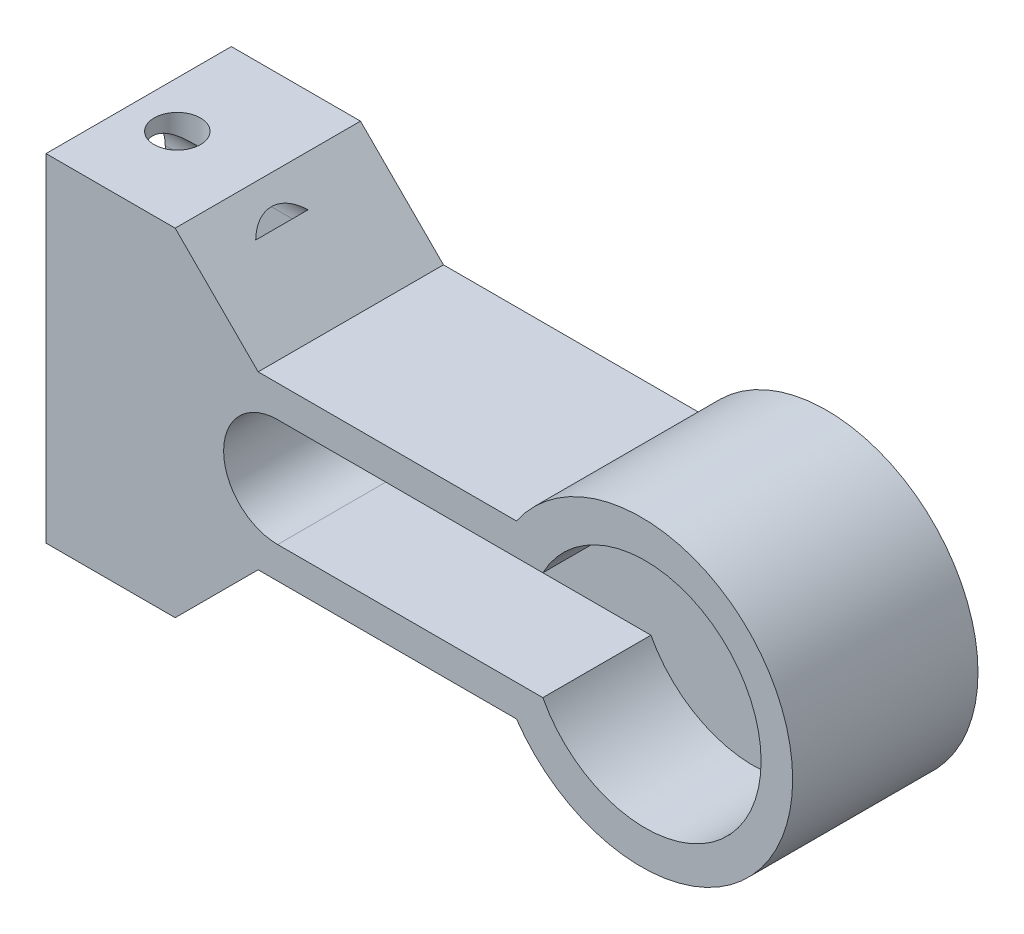
SolidWorks part; units mm, degrees
ref_plane "Front Plane" through (0, 0, 0) normal (0, 0, 1) x (1, 0, 0)
ref_plane "Top Plane" through (0, 0, 0) normal (0, 1, 0) x (1, 0, 0)
ref_plane "Right Plane" through (0, 0, 0) normal (1, 0, 0) x (0, 0, -1)
sketch "Sketch1" plane through (0, 0, 0) normal (0, 0, 1) x (1, 0, 0)
  line L1 (25, -15) -> (-25, -15)
  line L2 (25, -15) -> (25, 15)
  line L3 (25, 15) -> (-25, 15)
  line L4 (-25, -15) -> (-25, 15)
  line L5 (25, -15) -> (-25, 15) construction
  line L6 (25, 15) -> (-25, -15) construction
  point P0 (0, 0)
  dimension "D1" = 30
  dimension "D2" = 50
extrude "Boss-Extrude1" add sketch "Sketch1" along normal blind 15
sketch "Sketch2" plane through (-25, 0, 0) normal (-1, 0, 0) x (0, 0, 1)
  line L0 (6.7287, 7.5168) -> (6.7287, -7.9271) construction
  line L1 (9.1787, 7.5168) -> (9.1787, -7.9271)
  line L2 (4.2787, 7.5168) -> (4.2787, -7.9271)
  arc A0 (9.1787, 7.5168) -> (4.2787, 7.5168) centre (6.7287, 7.5168) ccw
  arc A1 (4.2787, -7.9271) -> (9.1787, -7.9271) centre (6.7287, -7.9271) ccw
  circle A2 centre (6.7287, -0.2052) radius 4.5
  point P2 (6.7287, -0.2052)
  dimension "D1" = 2.45
extrude "Cut-Extrude1" cut sketch "Sketch2" against normal blind 10
sketch "Sketch4" plane through (0, 0, 15) normal (0, 0, 1) x (1, 0, 0)
  line L0 (-10, 0) -> (13.8, 0) construction
  line L1 (-10, 3.5) -> (13.8, 3.5)
  line L2 (-10, -3.5) -> (13.8, -3.5)
  line L3 (25, -15) -> (25, 15) construction
  arc A0 (-10, 3.5) -> (-10, -3.5) centre (-10, 0) ccw
  arc A1 (13.8, -3.5) -> (13.8, 3.5) centre (13.8, 0) ccw
  circle A2 centre (13.8, 0) radius 7.5
  point P3 (1.9, 0)
  dimension "D1" = 3.5
  dimension "D2" = 23.8
  dimension "D3" = 35
extrude "Cut-Extrude3" cut sketch "Sketch4" against normal blind 10
sketch "Sketch5" plane through (0, 0, 5) normal (0, 0, 1) x (1, 0, 0)
  circle A0 centre (-10.0531, 0) radius 1.25
  circle A1 centre (-6.0531, 0) radius 1.25
  dimension "D1" = 4
extrude "Cut-Extrude4" cut sketch "Sketch5" against normal blind 10
sketch "Sketch7" plane through (0, 0, 15) normal (0, 0, 1) x (1, 0, 0)
  line L1 (-25, 15) -> (25, 15)
  line L2 (-25, 15) -> (-25, -15)
  line L3 (-25, -15) -> (25, -15)
  line L4 (25, 15) -> (25, -15)
extrude "Cut-Extrude5" cut sketch "Sketch7" against normal blind 3
sketch "Sketch8" plane through (0, 0, 12) normal (0, 0, 1) x (1, 0, 0)
  line L0 (-25, 10.9223) -> (-16.6371, 10.9223)
  line L1 (-25, 15) -> (-25, -15) construction
  line L2 (-16.6371, 10.9223) -> (-11.265, 5.5502)
  line L3 (-11.265, 5.5502) -> (5.5467, 5.5502)
  line L4 (-25, 10.9223) -> (-25, -10.9223)
  line L6 (-11.265, -5.5502) -> (5.5467, -5.5502)
  line L7 (-16.6371, -10.9223) -> (-11.265, -5.5502)
  line L8 (-25, -10.9223) -> (-16.6371, -10.9223)
  line L9 (-25, 15) -> (25, 15)
  line L10 (-25, 15) -> (-25, -15)
  line L11 (-25, -15) -> (25, -15)
  line L12 (25, 15) -> (25, -15)
  arc A0 (5.4598, -5.5502) -> (5.4598, 5.5502) centre (13.5402, 0) ccw
  line M9 (-25, 15) -> (-25, -15)
  line M10 (-25, -15) -> (25, -15)
  line M11 (25, -15) -> (25, 15)
  line M12 (25, 15) -> (-25, 15)
extrude "Cut-Extrude6" cut sketch "Sketch8" against normal blind 13 contours A0 L6 L7 L8 L0 L2 L3 M9 M10 M11 M12
sketch "Sketch9" plane through (0, 10.9223, 0) normal (0, 1, 0) x (1, 0, 0)
  line L0 (-25, 0) -> (-16.6371, 0) construction
  line L1 (-25, 0) -> (-25, -12) construction
  circle A0 centre (-22, -6.5) radius 1.5
  point P4 (0, 0)
  dimension "D1" = 6.5
  dimension "D2" = 3
extrude "Cut-Extrude7" cut sketch "Sketch9" against normal blind 23
